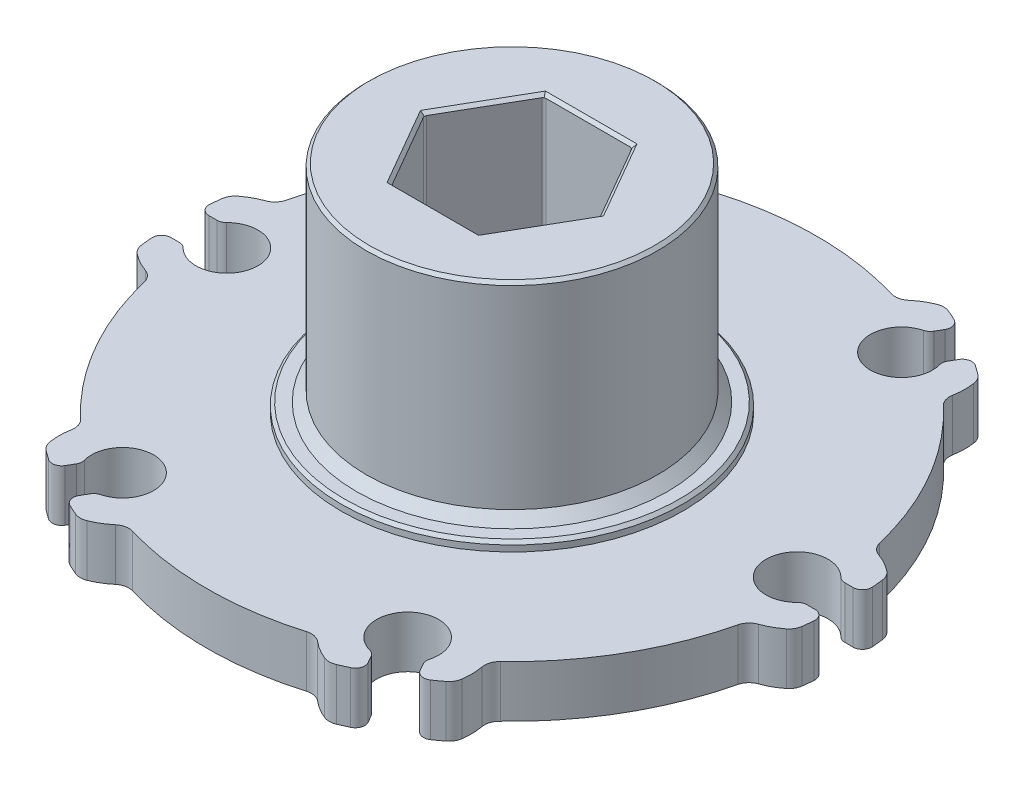
SolidWorks part; units mm, degrees
ref_plane "Front Plane" through (0, 0, 0) normal (0, 0, 1) x (1, 0, 0)
ref_plane "Top Plane" through (0, 0, 0) normal (0, 1, 0) x (1, 0, 0)
ref_plane "Right Plane" through (0, 0, 0) normal (1, 0, 0) x (0, 0, -1)
sketch "Sketch1" plane through (0, 0, 0) normal (0, 0, 1) x (1, 0, 0)
  line L0 (27.7876, 7.366) -> (0, 7.366)
  line L1 (0, 7.366) -> (0, 3.048)
  line L2 (0, 3.048) -> (27.7876, 3.048)
  line L3 (27.7876, 3.048) -> (27.7876, 7.366)
  line L4 (0, 7.366) -> (0, 3.048) construction
revolve "Revolve1" add sketch "Sketch1" angle 360 about L4
sketch "Sketch2" plane through (0, 7.366, 0) normal (0, 1, 0) x (-1, 0, 0)
  line L0 (27.7422, 1.5875) -> (25.86, 1.5875)
  line L1 (25.86, -1.5875) -> (27.7422, -1.5875)
  arc A0 (25.86, 1.5875) -> (25.86, -1.5875) centre (23.8125, 0) cw
  arc A1 (27.7422, -1.5875) -> (27.7422, 1.5875) centre (0, 0) ccw
extrude "Cut-Extrude1" cut sketch "Sketch2" against normal through all
sketch "Sketch3" plane through (0, 7.366, 0) normal (0, 1, 0) x (-1, 0, 0)
  arc A0 (27.522, -3.8329) -> (24.9505, -5.2112) centre (23.8125, 0) cw
  arc A1 (24.9505, -5.2112) -> (16.9883, -19.0022) centre (0, 0) cw
  arc A2 (16.9883, -19.0022) -> (17.0804, -21.9183) centre (11.9062, -20.6222) cw
  arc A3 (17.0804, -21.9183) -> (27.522, -3.8329) centre (0, 0) ccw
extrude "Cut-Extrude2" cut sketch "Sketch3" against normal through all
sketch "Sketch4" plane through (0, 7.366, 0) normal (0, 1, 0) x (-1, 0, 0)
  line L0 (15.2459, -23.2317) -> (14.3048, -21.6016)
  line L1 (11.5552, -23.1891) -> (12.4963, -24.8192)
  arc A0 (14.3048, -21.6016) -> (11.5552, -23.1891) centre (11.9063, -20.6222) cw
  arc A1 (12.4963, -24.8192) -> (15.2459, -23.2317) centre (0, 0) ccw
extrude "Cut-Extrude3" cut sketch "Sketch4" against normal through all
sketch "Sketch5" plane through (0, 7.366, 0) normal (0, 1, 0) x (-1, 0, 0)
  arc A0 (10.4416, -25.7512) -> (7.9622, -24.2134) centre (11.9063, -20.6222) cw
  arc A1 (7.9622, -24.2134) -> (-7.9622, -24.2134) centre (0, 0) cw
  arc A2 (-7.9622, -24.2134) -> (-10.4416, -25.7512) centre (-11.9063, -20.6222) cw
  arc A3 (-10.4416, -25.7512) -> (10.4416, -25.7512) centre (0, 0) ccw
extrude "Cut-Extrude4" cut sketch "Sketch5" against normal through all
sketch "Sketch6" plane through (0, 7.366, 0) normal (0, 1, 0) x (-1, 0, 0)
  line L0 (-12.4963, -24.8192) -> (-11.5552, -23.1891)
  line L1 (-14.3048, -21.6016) -> (-15.2459, -23.2317)
  arc A0 (-11.5552, -23.1891) -> (-14.3048, -21.6016) centre (-11.9062, -20.6222) cw
  arc A1 (-15.2459, -23.2317) -> (-12.4963, -24.8192) centre (0, 0) ccw
extrude "Cut-Extrude5" cut sketch "Sketch6" against normal through all
sketch "Sketch7" plane through (0, 7.366, 0) normal (0, 1, 0) x (-1, 0, 0)
  arc A0 (-17.0804, -21.9183) -> (-16.9883, -19.0022) centre (-11.9062, -20.6222) cw
  arc A1 (-16.9883, -19.0022) -> (-24.9505, -5.2112) centre (0, 0) cw
  arc A2 (-24.9505, -5.2112) -> (-27.522, -3.8329) centre (-23.8125, 0) cw
  arc A3 (-27.522, -3.8329) -> (-17.0804, -21.9183) centre (0, 0) ccw
extrude "Cut-Extrude6" cut sketch "Sketch7" against normal through all
sketch "Sketch8" plane through (0, 7.366, 0) normal (0, 1, 0) x (-1, 0, 0)
  line L0 (-27.7422, -1.5875) -> (-25.86, -1.5875)
  line L1 (-25.86, 1.5875) -> (-27.7422, 1.5875)
  arc A0 (-25.86, -1.5875) -> (-25.86, 1.5875) centre (-23.8125, 0) cw
  arc A1 (-27.7422, 1.5875) -> (-27.7422, -1.5875) centre (0, 0) ccw
extrude "Cut-Extrude7" cut sketch "Sketch8" against normal through all
sketch "Sketch9" plane through (0, 7.366, 0) normal (0, 1, 0) x (-1, 0, 0)
  arc A0 (-27.522, 3.8329) -> (-24.9505, 5.2112) centre (-23.8125, 0) cw
  arc A1 (-24.9505, 5.2112) -> (-16.9883, 19.0022) centre (0, 0) cw
  arc A2 (-16.9883, 19.0022) -> (-17.0804, 21.9183) centre (-11.9062, 20.6222) cw
  arc A3 (-17.0804, 21.9183) -> (-27.522, 3.8329) centre (0, 0) ccw
extrude "Cut-Extrude8" cut sketch "Sketch9" against normal through all
sketch "Sketch10" plane through (0, 7.366, 0) normal (0, 1, 0) x (-1, 0, 0)
  line L0 (-15.2459, 23.2317) -> (-14.3048, 21.6016)
  line L1 (-11.5552, 23.1891) -> (-12.4963, 24.8192)
  arc A0 (-14.3048, 21.6016) -> (-11.5552, 23.1891) centre (-11.9063, 20.6222) cw
  arc A1 (-12.4963, 24.8192) -> (-15.2459, 23.2317) centre (0, 0) ccw
extrude "Cut-Extrude9" cut sketch "Sketch10" against normal through all
sketch "Sketch11" plane through (0, 7.366, 0) normal (0, 1, 0) x (-1, 0, 0)
  arc A0 (-10.4416, 25.7512) -> (-7.9622, 24.2134) centre (-11.9062, 20.6222) cw
  arc A1 (-7.9622, 24.2134) -> (7.9622, 24.2134) centre (0, 0) cw
  arc A2 (7.9622, 24.2134) -> (10.4416, 25.7512) centre (11.9063, 20.6222) cw
  arc A3 (10.4416, 25.7512) -> (-10.4416, 25.7512) centre (0, 0) ccw
extrude "Cut-Extrude10" cut sketch "Sketch11" against normal through all
sketch "Sketch12" plane through (0, 7.366, 0) normal (0, 1, 0) x (-1, 0, 0)
  line L0 (12.4963, 24.8192) -> (11.5552, 23.1891)
  line L1 (14.3048, 21.6016) -> (15.2459, 23.2317)
  arc A0 (11.5552, 23.1891) -> (14.3048, 21.6016) centre (11.9062, 20.6222) cw
  arc A1 (15.2459, 23.2317) -> (12.4963, 24.8192) centre (0, 0) ccw
extrude "Cut-Extrude11" cut sketch "Sketch12" against normal through all
sketch "Sketch13" plane through (0, 7.366, 0) normal (0, 1, 0) x (-1, 0, 0)
  arc A0 (17.0804, 21.9183) -> (16.9883, 19.0022) centre (11.9062, 20.6222) cw
  arc A1 (16.9883, 19.0022) -> (24.9505, 5.2112) centre (0, 0) cw
  arc A2 (24.9505, 5.2112) -> (27.522, 3.8329) centre (23.8125, 0) cw
  arc A3 (27.522, 3.8329) -> (17.0804, 21.9183) centre (0, 0) ccw
extrude "Cut-Extrude12" cut sketch "Sketch13" against normal through all
sketch "Sketch14" plane through (0, 3.048, 0) normal (0, -1, 0) x (1, 0, 0)
  circle A0 centre (0, 0) radius 14.2748
extrude "Boss-Extrude1" add sketch "Sketch14" along normal blind 1.524
sketch "Sketch15" plane through (0, 1.524, 0) normal (0, -1, 0) x (1, 0, 0)
  circle A0 centre (0, 0) radius 9.2382
extrude "Boss-Extrude2" add sketch "Sketch15" along normal blind 1.524
sketch "Sketch16" plane through (0, 7.366, 0) normal (0, 1, 0) x (-1, 0, 0)
  circle A0 centre (0, 0) radius 14.2748
extrude "Boss-Extrude3" add sketch "Sketch16" along normal blind 0.762
sketch "Sketch17" plane through (0, 8.128, 0) normal (0, 1, 0) x (-1, 0, 0)
  circle A0 centre (0, 0) radius 12.1666
extrude "Boss-Extrude4" add sketch "Sketch17" along normal blind 17.272
sketch "Sketch18" plane through (0, 25.4, 0) normal (0, 1, 0) x (-1, 0, 0)
  line L0 (-3.6735, -6.3627) -> (3.6735, -6.3627)
  line L1 (3.6735, -6.3627) -> (7.347, 0)
  line L2 (7.347, 0) -> (3.6735, 6.3627)
  line L3 (3.6735, 6.3627) -> (-3.6735, 6.3627)
  line L4 (-3.6735, 6.3627) -> (-7.347, 0)
  line L5 (-7.347, 0) -> (-3.6735, -6.3627)
extrude "Cut-Extrude13" cut sketch "Sketch18" against normal through all
ref_plane "Plane1" through (0, 0, 0) normal (0, 0, -1) x (-1, 0, 0)
sketch "Sketch19" plane through (0, 0, 0) normal (0, 0, -1) x (-1, 0, 0)
  line L0 (21.2217, 3.048) -> (23.8125, 3.048)
  line L1 (23.8125, 3.048) -> (23.8125, 7.366)
  line L2 (23.8125, 7.366) -> (21.2217, 7.366)
  line L3 (21.2217, 7.366) -> (21.2217, 3.048)
  line L4 (23.8125, 3.048) -> (23.8125, 7.366) construction
revolve "Cut-Revolve1" cut sketch "Sketch19" angle 360 about L4
ref_plane "Plane2" through (0, 0, -20.6222) normal (0, 0, -1) x (-1, 0, 0)
sketch "Sketch20" plane through (0, 0, -20.6222) normal (0, 0, -1) x (-1, 0, 0)
  line L0 (9.3155, 3.048) -> (11.9063, 3.048)
  line L1 (11.9063, 3.048) -> (11.9063, 7.366)
  line L2 (11.9063, 7.366) -> (9.3155, 7.366)
  line L3 (9.3155, 7.366) -> (9.3155, 3.048)
  line L4 (11.9063, 3.048) -> (11.9063, 7.366) construction
revolve "Cut-Revolve2" cut sketch "Sketch20" angle 360 about L4
sketch "Sketch21" plane through (0, 0, -20.6222) normal (0, 0, -1) x (-1, 0, 0)
  line L0 (-14.497, 3.048) -> (-11.9062, 3.048)
  line L1 (-11.9062, 3.048) -> (-11.9062, 7.366)
  line L2 (-11.9062, 7.366) -> (-14.497, 7.366)
  line L3 (-14.497, 7.366) -> (-14.497, 3.048)
  line L4 (-11.9062, 3.048) -> (-11.9062, 7.366) construction
revolve "Cut-Revolve3" cut sketch "Sketch21" angle 360 about L4
sketch "Sketch22" plane through (0, 0, 0) normal (0, 0, -1) x (-1, 0, 0)
  line L0 (-26.4033, 3.048) -> (-23.8125, 3.048)
  line L1 (-23.8125, 3.048) -> (-23.8125, 7.366)
  line L2 (-23.8125, 7.366) -> (-26.4033, 7.366)
  line L3 (-26.4033, 7.366) -> (-26.4033, 3.048)
  line L4 (-23.8125, 3.048) -> (-23.8125, 7.366) construction
revolve "Cut-Revolve4" cut sketch "Sketch22" angle 360 about L4
ref_plane "Plane3" through (0, 0, 20.6222) normal (0, 0, -1) x (-1, 0, 0)
sketch "Sketch23" plane through (0, 0, 20.6222) normal (0, 0, -1) x (-1, 0, 0)
  line L0 (-14.4971, 3.048) -> (-11.9063, 3.048)
  line L1 (-11.9063, 3.048) -> (-11.9063, 7.366)
  line L2 (-11.9063, 7.366) -> (-14.4971, 7.366)
  line L3 (-14.4971, 7.366) -> (-14.4971, 3.048)
  line L4 (-11.9063, 3.048) -> (-11.9063, 7.366) construction
revolve "Cut-Revolve5" cut sketch "Sketch23" angle 360 about L4
sketch "Sketch24" plane through (0, 0, 20.6222) normal (0, 0, -1) x (-1, 0, 0)
  line L0 (9.3154, 3.048) -> (11.9062, 3.048)
  line L1 (11.9062, 3.048) -> (11.9062, 7.366)
  line L2 (11.9062, 7.366) -> (9.3154, 7.366)
  line L3 (9.3154, 7.366) -> (9.3154, 3.048)
  line L4 (11.9062, 3.048) -> (11.9062, 7.366) construction
revolve "Cut-Revolve6" cut sketch "Sketch24" angle 360 about L4
chamfer "Chamfer1" distance 0.254 angle 45 16 edges at (0, 8.128, 14.2748) (5.5103, 25.4, -3.1814) (0, 25.4, -6.3627) (-5.5103, 25.4, -3.1813) (-5.5103, 25.4, 3.1814) (0, 25.4, 6.3627) (5.5103, 25.4, 3.1813) (0, 1.524, -14.2748) (0, 0, -9.2382) (-5.5103, 0, 3.1814) (0, 0, 6.3627) (5.5103, 0, 3.1813) (5.5103, 0, -3.1814) (0, 0, -6.3627) (-5.5103, 0, -3.1813) (0, 25.4, 12.1666)
chamfer "Chamfer2" distance 0.8128 angle 45 1 edges at (0, 8.128, 12.1666)
fillet "Fillet1" radius 0.254 6 edges at (7.347, 12.7, 0) (-3.6735, 12.7, 6.3627) (3.6735, 12.7, 6.3627) (-3.6735, 12.7, -6.3627) (3.6735, 12.7, -6.3627) (-7.347, 12.7, 0)
fillet "Fillet2" radius 0.7874 24 edges at (-27.7422, 5.207, -1.5875) (-14.3048, 5.207, 21.6016) (12.4963, 5.207, 24.8192) (-11.5552, 5.207, 23.1891) (11.5552, 5.207, -23.1891) (12.4963, 5.207, -24.8192) (-14.3048, 5.207, -21.6016) (-15.2459, 5.207, 23.2317) (-25.86, 5.207, 1.5875) (11.5552, 5.207, 23.1891) (14.3048, 5.207, -21.6016) (14.3048, 5.207, 21.6016) (27.7422, 5.207, -1.5875) (-12.4963, 5.207, 24.8192) (-11.5552, 5.207, -23.1891) (-12.4963, 5.207, -24.8192) (-27.7422, 5.207, 1.5875) (25.86, 5.207, 1.5875) (-25.86, 5.207, -1.5875) (25.86, 5.207, -1.5875) (15.2459, 5.207, 23.2317) (-15.2459, 5.207, -23.2317) (27.7422, 5.207, 1.5875) (15.2459, 5.207, -23.2317)
fillet "Fillet3" radius 1.27 24 edges at (16.9883, 5.207, 19.0022) (-24.9505, 5.207, 5.2112) (7.9622, 5.207, -24.2134) (-10.4416, 5.207, 25.7512) (-7.9622, 5.207, 24.2134) (10.4416, 5.207, 25.7512) (24.9505, 5.207, -5.2112) (17.0804, 5.207, 21.9183) (-16.9883, 5.207, -19.0022) (27.522, 5.207, 3.8329) (-16.9883, 5.207, 19.0022) (27.522, 5.207, -3.8329) (7.9622, 5.207, 24.2134) (17.0804, 5.207, -21.9183) (24.9505, 5.207, 5.2112) (10.4416, 5.207, -25.7512) (16.9883, 5.207, -19.0022) (-10.4416, 5.207, -25.7512) (-7.9622, 5.207, -24.2134) (-17.0804, 5.207, -21.9183) (-24.9505, 5.207, -5.2112) (-27.522, 5.207, -3.8329) (-27.522, 5.207, 3.8329) (-17.0804, 5.207, 21.9183)
